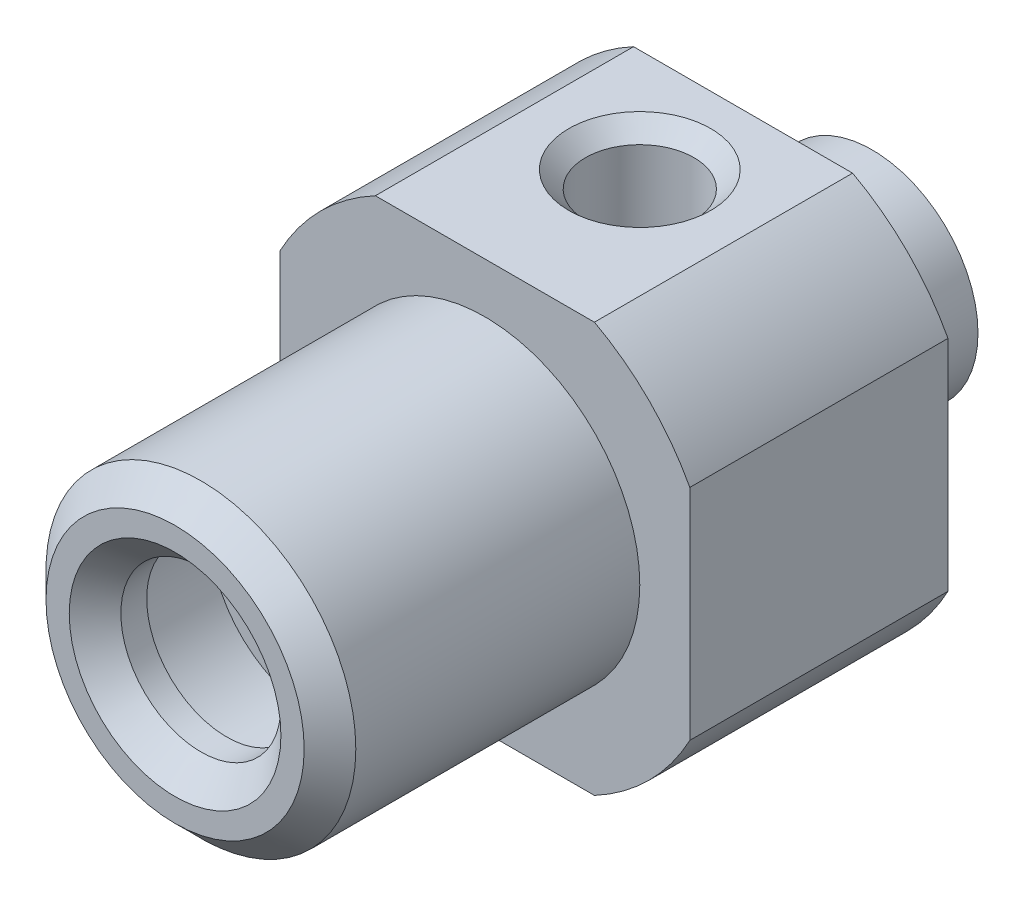
SolidWorks part; units mm, degrees
ref_plane "Front Plane" through (0, 0, 0) normal (0, 0, 1) x (1, 0, 0)
ref_plane "Top Plane" through (0, 0, 0) normal (0, 1, 0) x (1, 0, 0)
ref_plane "Right Plane" through (0, 0, 0) normal (1, 0, 0) x (0, 0, -1)
sketch "Sketch1" plane through (0, 0, 0) normal (1, 0, 0) x (0, 0, -1)
  line L0 (0, 0) -> (0, 5390.1232) construction
  line L1 (0, 0) -> (5390.1232, 0) construction
  line L2 (-12.5, 3.1) -> (-13.5, 4.1)
  line L3 (-13.5, 4.1) -> (-13.5, 5)
  line L4 (-13.5, 5) -> (-12.5, 6)
  line L5 (-12.5, 6) -> (-1.5, 6)
  line L6 (-1.5, 6) -> (-1.5, 9)
  line L7 (-1.5, 9) -> (8.5, 9)
  line L8 (8.5, 9) -> (8.5, 4.75)
  line L9 (8.5, 4.75) -> (9.85, 4.75)
  line L10 (9.85, 4.75) -> (9.85, 4.1)
  line L11 (9.85, 4.1) -> (13.5, 4.1)
  line L12 (13.5, 4.1) -> (13.5, 2.25)
  line L13 (13.5, 2.25) -> (-8, 2.25)
  line L14 (-11.5, 3.1) -> (-11.5, 4.15)
  line L15 (-11.5, 4.15) -> (-8, 4.15)
  line L16 (-8, 4.15) -> (-8, 2.25)
  line L17 (-11.5, 3.1) -> (-12.5, 3.1)
  dimension "D1" = 12
  dimension "D2" = 6.2
  dimension "D3" = 8.3
  dimension "D4" = 18
  dimension "D5" = 9.5
  dimension "D6" = 8.2
  dimension "D7" = 1.35
  dimension "D8" = 5
  dimension "D9" = 10
  dimension "D10" = 4.5
  dimension "D11" = 12
  dimension "D12" = 1
  dimension "D13" = 45
  dimension "D14" = 1
  dimension "D15" = 45
  dimension "D16" = 3.5
  dimension "D17" = 5.5
revolve "Revolve1" add sketch "Sketch1" angle 360 about L1
cosmetic thread "Cosmetic Thread1" parameters "D2"=10.619
sketch "Sketch2" plane through (0, 0, -8.5) normal (0, 0, -1) x (-1, 0, 0)
  line L1 (-7.9375, 7.9375) -> (7.9375, 7.9375)
  line L2 (-7.9375, 7.9375) -> (-7.9375, -7.9375)
  line L3 (-7.9375, -7.9375) -> (7.9375, -7.9375)
  line L4 (7.9375, 7.9375) -> (7.9375, -7.9375)
  line L5 (-7.9375, 7.9375) -> (7.9375, -7.9375) construction
  line L6 (-7.9375, -7.9375) -> (7.9375, 7.9375) construction
  point P0 (0, 0)
  circle M5 centre (0, 0) radius 9
  dimension "D1" = 15.875
extrude "Cut-Extrude2" cut sketch "Sketch2" against normal up to next contours L1 M5 | L2 M5 | L3 M5 | L4 M5
hole_wizard "M5x0.8 Tapped Hole1" positions "Sketch3" profile "Sketch4" tap size "M5x0.8" standard "JIS"
sketch "Sketch3" plane through (0, 7.9375, 0) normal (0, 1, 0) x (1, 0, 0)
  line L0 (0, 4.5) -> (0, 0) construction
  line L2 (4.2422, 8.5) -> (-4.2422, 8.5) construction
  point P0 (0, 4.5)
  dimension "D1" = 4
sketch "Sketch4" plane through (0, 7.9375, -4.5) normal (1, 0, 0) x (0, 0, 1)
  line L0 (0, 0) -> (0, 7)
  line L1 (0, 7) -> (2.1, 7)
  line L2 (2.1, 7) -> (2.1, 0.65)
  line L3 (2.1, 0.65) -> (2.75, 0)
  line L5 (2.75, 0) -> (0, 0)
  line L6 (-2.1, 0.65) -> (-2.75, 0) construction
  line L10 (0, 7) -> (-2.1, 7) construction
  line L11 (0, -6.35) -> (0, 107.95) construction
  dimension "Tap Drill Dia." = 4.2
  dimension "Tap Drill Depth" = 7
  dimension "Near C'Sink Dia." = 5.5
  dimension "Near C'Sink Angle" = 90
  dimension "Drill Angle" = 180
cosmetic thread "Hole Thread2" parameters "D1"=6, "D2"=5
ref_plane "Plane1" [suppressed] through (0, 15.5, 0) normal (0, 1, 0) x (1, 0, 0)
sketch "Sketch5" [suppressed] plane through (0, 15.5, 0) normal (0, 1, 0) x (1, 0, 0)
  line L0 (0, 0) -> (0, 50000) construction
  line L1 (0, 0) -> (50000, 0) construction
  line L2 (13.5, 14.75) -> (-13.5, 14.75) construction
  line L3 (-7.75, 14.75) -> (7.75, 14.75)
  line L4 (-7.75, 14.75) -> (-7.75, -0.75)
  line L5 (-7.75, -0.75) -> (7.75, -0.75)
  line L6 (7.75, 14.75) -> (7.75, -0.75)
  line L7 (-13.5, -0.75) -> (13.5, -0.75) construction
  dimension "D1" = 16.7946
extrude "Boss-Extrude1" [suppressed] add sketch "Sketch5" against normal up to surface (4.4462 mm away)
sketch "Sketch6" [suppressed] plane through (0, 0, 0) normal (1, 0, 0) x (0, 0, -1)
  line L0 (-19.9481, 0) -> (3.2487, 0) construction
  line L1 (-0.75, 10) -> (-2.25, 10)
  line L2 (-0.75, 11) -> (-0.75, -11) construction
  line L3 (-2.25, 10) -> (-5.7898, 13.5398)
  line L4 (-5.7898, 13.5398) -> (-0.75, 13.5398)
  line L5 (-0.75, 11.0538) -> (-0.75, -13.5) construction
  line L6 (-0.75, 13.5398) -> (-0.75, 10)
  dimension "D1" = 13.2321
  dimension "D2" = 1.0568
  dimension "D3" = 40.601
revolve "Cut-Revolve1" [suppressed] cut sketch "Sketch6" angle 360 about L0
hole_wizard "M5x0.8 Tapped Hole2" [suppressed] positions "Sketch7" profile "Sketch8" tap size "M5x0.8" standard "JIS"
sketch "Sketch7" plane through (0, 15.5, 0) normal (0, 1, 0) x (1, 0, 0)
  line L0 (0, 0) -> (0, 6.25) construction
  line L2 (10.6, 15.1) -> (-10.6, 15.1) construction
  point P0 (0, 6.25)
  dimension "D1" = 6.0393
sketch "Sketch8" plane through (0, 15.5, -6.25) normal (1, 0, 0) x (0, 0, 1)
  line L0 (0, 0) -> (0, 8)
  line L1 (0, 8) -> (2.1, 8)
  line L2 (2.1, 8) -> (2.1, 0.425)
  line L3 (2.1, 0.425) -> (2.525, 0)
  line L5 (2.525, 0) -> (0, 0)
  line L6 (-2.1, 0.425) -> (-2.525, 0) construction
  line L10 (0, 8) -> (-2.1, 8) construction
  line L11 (0, -6.35) -> (0, 107.95) construction
  dimension "Tap Drill Dia." = 4.2
  dimension "Tap Drill Depth" = 8
  dimension "Near C'Sink Dia." = 5.05
  dimension "Near C'Sink Angle" = 90
  dimension "Drill Angle" = 180
cosmetic thread "Hole Thread3" [suppressed] parameters "D1"=6.5, "D2"=5
hole_wizard "G1/8 Tapped Hole1" [suppressed] positions "Sketch9" profile "Sketch10" tap size "G1/8" standard "JIS"
sketch "Sketch9" plane through (0, 15.5, 0) normal (0, 1, 0) x (1, 0, 0)
  line L0 (13.1, 16.1) -> (-13.1, 16.1) construction
  line L1 (0, 6.8) -> (0, 0) construction
  point P0 (0, 6.8)
  dimension "D1" = 9.0659
sketch "Sketch10" plane through (0, 15.5, -6.8) normal (1, 0, 0) x (0, 0, 1)
  line L0 (0, 0) -> (0, 10)
  line L1 (0, 10) -> (4.4, 10)
  line L2 (4.4, 10) -> (4.4, 0.489)
  line L3 (4.4, 0.489) -> (4.889, 0)
  line L5 (4.889, 0) -> (0, 0)
  line L6 (-4.4, 0.489) -> (-4.889, 0) construction
  line L10 (0, 10) -> (-4.4, 10) construction
  line L11 (0, -6.35) -> (0, 107.95) construction
  dimension "Tap Drill Dia." = 8.8
  dimension "Tap Drill Depth" = 10
  dimension "Near C'Sink Dia." = 9.778
  dimension "Near C'Sink Angle" = 90
  dimension "Drill Angle" = 180
cosmetic thread "Hole Thread4" [suppressed] parameters "D1"=8, "D2"=9.728
